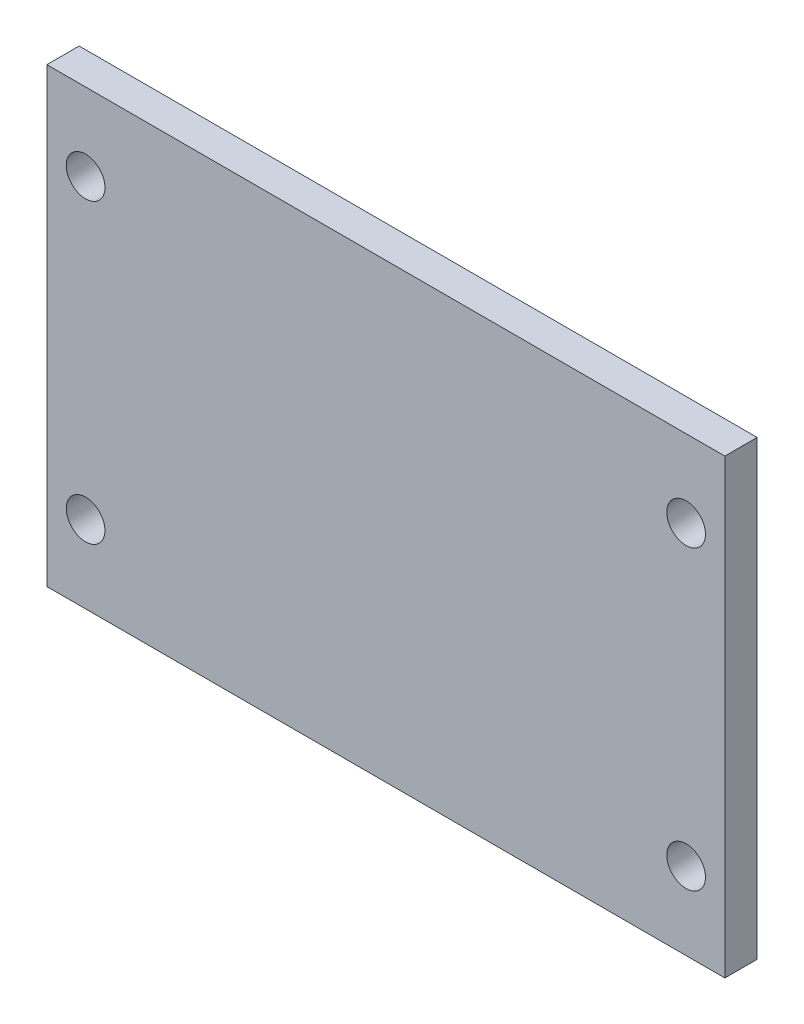
SolidWorks part; units mm, degrees
ref_plane "Front Plane" through (0, 0, 0) normal (0, 0, 1) x (1, 0, 0)
ref_plane "Top Plane" through (0, 0, 0) normal (0, 1, 0) x (1, 0, 0)
ref_plane "Right Plane" through (0, 0, 0) normal (1, 0, 0) x (0, 0, -1)
sketch "Sketch1" plane through (0, 0, 0) normal (0, 0, 1) x (1, 0, 0)
  line L0 (0, 0) -> (0, 106.3954) construction
  line L1 (-52.5, 35) -> (52.5, 35)
  line L2 (-52.5, 35) -> (-52.5, -35)
  line L3 (-52.5, -35) -> (52.5, -35)
  line L4 (52.5, 35) -> (52.5, -35)
  line L5 (-100.1633, 0) -> (116.2332, 0) construction
  dimension "D1" = 105
  dimension "D2" = 70
  dimension "D3" = 35
extrude "Boss-Extrude1" add sketch "Sketch1" along normal mid plane 5
sketch "Sketch3" plane through (0, 0, 2.5) normal (0, 0, 1) x (1, 0, 0)
  line L0 (-67.2676, 0) -> (78.5686, 0) construction
  line L1 (0, 38.208) -> (0, -42.6208) construction
  point P0 (-46.5, 23)
  point P1 (-46.5, -23)
  point P2 (46.5, -23)
  point P3 (46.5, 23)
  dimension "D1" = 93
  dimension "D2" = 46
hole_wizard "Ø6.0mm Dowel Hole1" positions "Sketch6" profile "Sketch8" hole size "Ø6.0" standard "ISO" end condition through all
sketch "Sketch6" plane through (0, 0, 2.5) normal (0, 0, 1) x (1, 0, 0)
  point P0 (-46.5, 23)
  point P3 (-46.5, -23)
  point P6 (46.5, -23)
  point P9 (46.5, 23)
sketch "Sketch8" plane through (-46.5, 23, 2.5) normal (1, 0, 0) x (0, -1, 0)
  line L0 (0, 0) -> (0, 5)
  line L1 (0, 5) -> (3, 5)
  line L2 (3, 5) -> (3, 0)
  line L5 (3, 0) -> (0, 0)
  line L11 (0, -6.35) -> (0, 107.95) construction
  dimension "Thru Hole Dia." = 6
  dimension "Thru Hole Depth" = 5
